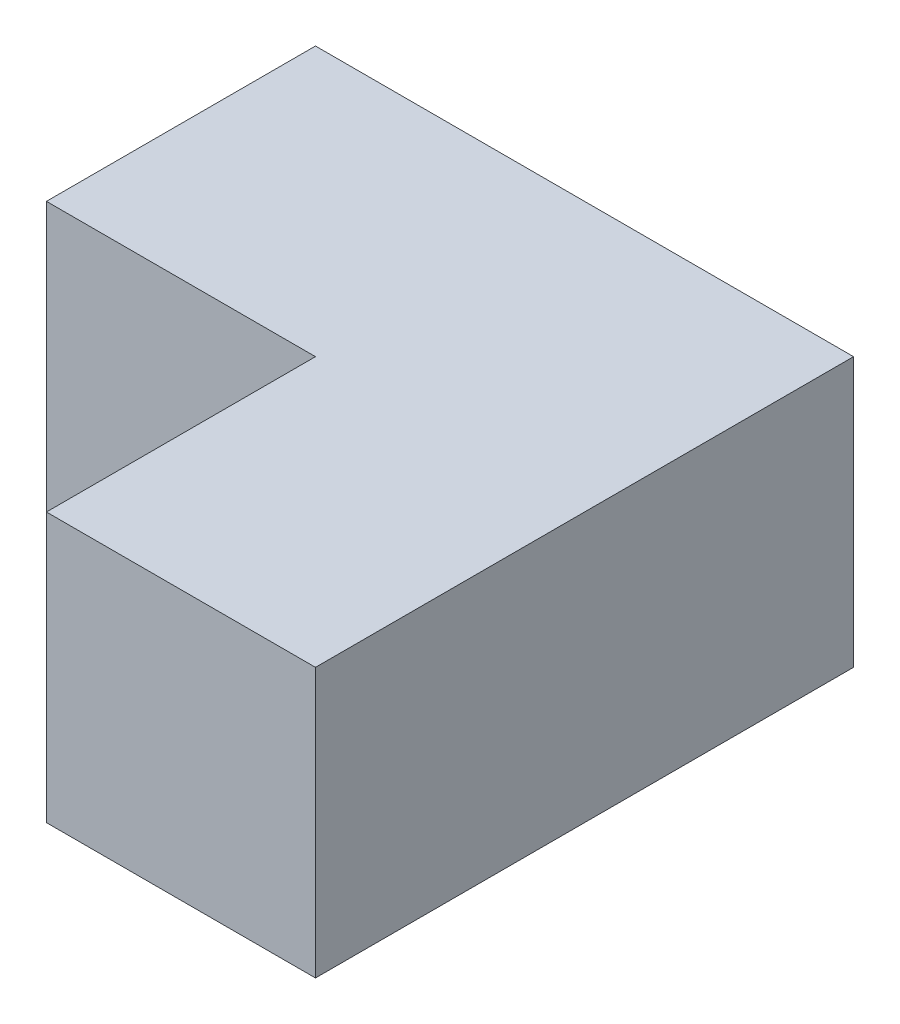
SolidWorks part; units mm, degrees
ref_plane "Front Plane" through (0, 0, 0) normal (0, 0, 1) x (1, 0, 0)
ref_plane "Top Plane" through (0, 0, 0) normal (0, 1, 0) x (1, 0, 0)
ref_plane "Right Plane" through (0, 0, 0) normal (1, 0, 0) x (0, 0, -1)
sketch "Sketch1" plane through (0, 0, 0) normal (0, 1, 0) x (1, 0, 0)
  line L1 (-25.4, -25.4) -> (25.4, -25.4)
  line L2 (-25.4, -25.4) -> (-25.4, 25.4)
  line L3 (-25.4, 25.4) -> (25.4, 25.4)
  line L4 (25.4, -25.4) -> (25.4, 25.4)
  line L5 (-25.4, -25.4) -> (25.4, 25.4) construction
  line L6 (-25.4, 25.4) -> (25.4, -25.4) construction
  point P0 (0, 0)
  dimension "D1" = 50.8
  dimension "D2" = 50.8
extrude "Boss-Extrude1" add sketch "Sketch1" along normal blind 25.4
sketch "Sketch2" plane through (0, 25.4, 0) normal (0, 1, 0) x (1, 0, 0)
  line L1 (-25.4, -25.4) -> (0, -25.4)
  line L2 (-25.4, -25.4) -> (-25.4, 0)
  line L3 (-25.4, 0) -> (0, 0)
  line L4 (0, -25.4) -> (0, 0)
extrude "Cut-Extrude1" cut sketch "Sketch2" against normal through all
